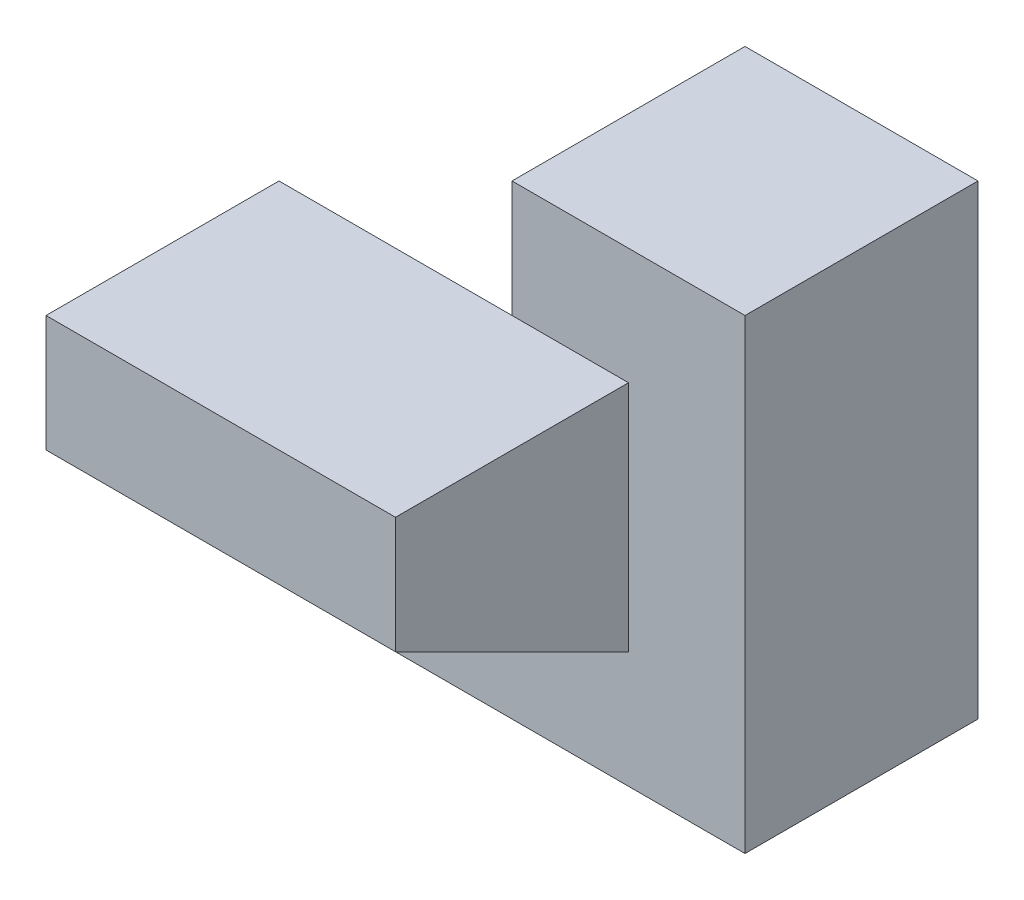
SolidWorks part; units mm, degrees
ref_plane "Front Plane" through (0, 0, 0) normal (0, 0, 1) x (1, 0, 0)
ref_plane "Top Plane" through (0, 0, 0) normal (0, 1, 0) x (1, 0, 0)
ref_plane "Right Plane" through (0, 0, 0) normal (1, 0, 0) x (0, 0, -1)
sketch "Sketch1" plane through (0, 0, 0) normal (1, 0, 0) x (0, 0, -1)
  line L1 (0, 0) -> (2, 0)
  line L2 (0, 0) -> (0, 4)
  line L3 (0, 4) -> (2, 4)
  line L4 (2, 0) -> (2, 4)
  dimension "D1" = 2
  dimension "D2" = 4
extrude "Boss-Extrude1" add sketch "Sketch1" along normal blind 2
sketch "Sketch2" plane through (0, 0, 0) normal (-1, 0, 0) x (0, 0, 1)
  line L0 (-2, 0) -> (0, 3)
  line L1 (0, 4) -> (0, 0) construction
  line L2 (0, 3) -> (2, 3)
  line L3 (2, 3) -> (2, 2)
  line L4 (2, 2) -> (0, 1)
  line L5 (0, 1) -> (0, 0)
  line L6 (0, 0) -> (-2, 0)
  dimension "D1" = 1
  dimension "D2" = 3
  dimension "D3" = 2
  dimension "D4" = 1
extrude "Boss-Extrude2" add sketch "Sketch2" along normal blind 2 and the other way blind 1
